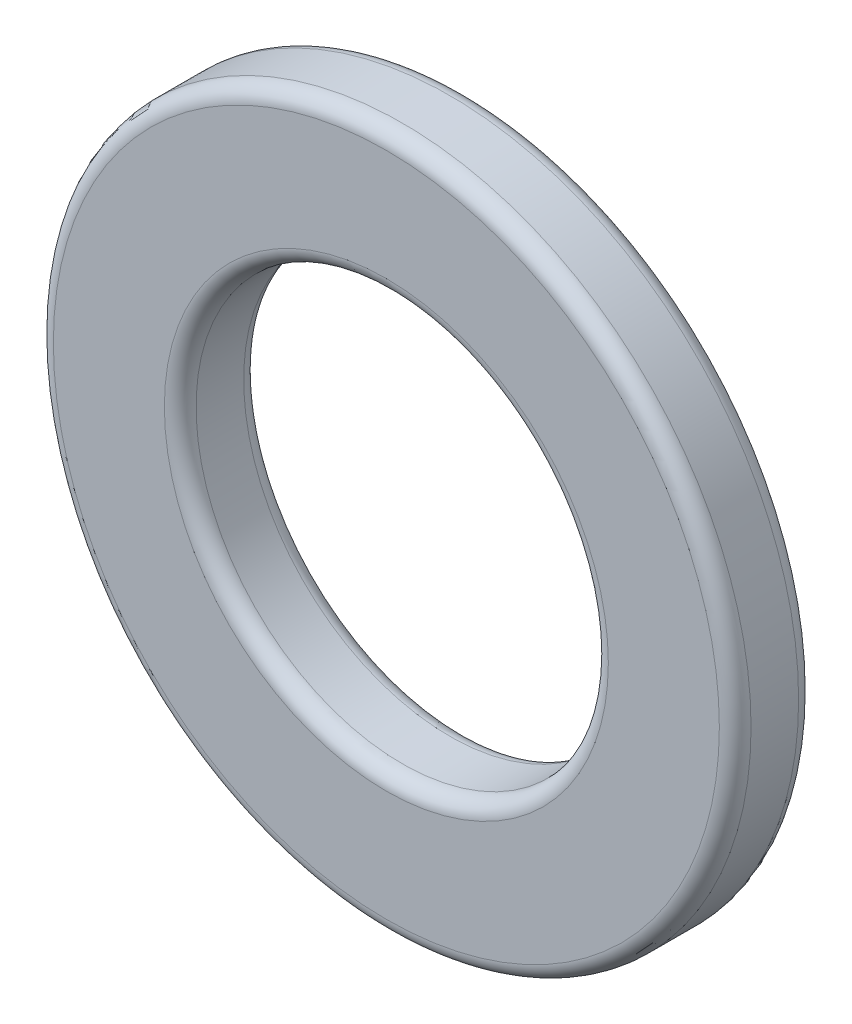
SolidWorks part; units mm, degrees
ref_plane "Front Plane" through (0, 0, 0) normal (0, 0, 1) x (1, 0, 0)
ref_plane "Top Plane" through (0, 0, 0) normal (0, 1, 0) x (1, 0, 0)
ref_plane "Right Plane" through (0, 0, 0) normal (1, 0, 0) x (0, 0, -1)
sketch "Sketch1" plane through (0, 0, 0) normal (0, 0, 1) x (1, 0, 0)
  circle A0 centre (0, 0) radius 6.5
  circle A1 centre (0, 0) radius 11
  dimension "D1" = 13
  dimension "D2" = 22
extrude "Boss-Extrude1" add sketch "Sketch1" along normal blind 2.5
fillet "Fillet1" radius 0.5 4 edges at (6.5, 0, 0) (11, 0, 0) (11, 0, 2.5) (6.5, 0, 2.5)
